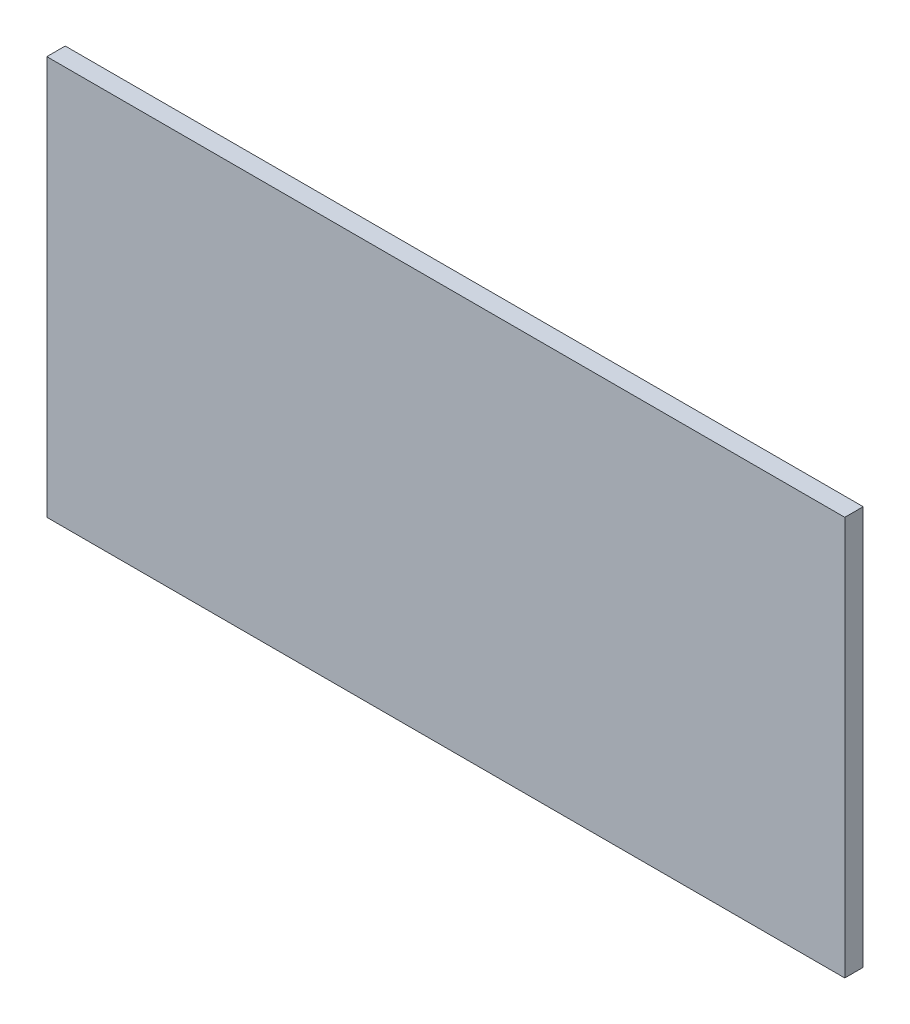
SolidWorks part; units mm, degrees
ref_plane "前视基准面" through (0, 0, 0) normal (0, 0, 1) x (1, 0, 0)
ref_plane "上视基准面" through (0, 0, 0) normal (0, 1, 0) x (1, 0, 0)
ref_plane "右视基准面" through (0, 0, 0) normal (1, 0, 0) x (0, 0, -1)
sketch "草图1" plane through (0, 0, 0) normal (0, 0, 1) x (1, 0, 0)
  line L1 (-65, 32.5) -> (65, 32.5)
  line L2 (-65, 32.5) -> (-65, -32.5)
  line L3 (-65, -32.5) -> (65, -32.5)
  line L4 (65, 32.5) -> (65, -32.5)
  line L5 (-65, 32.5) -> (65, -32.5) construction
  line L6 (-65, -32.5) -> (65, 32.5) construction
  point P0 (0, 0)
  dimension "D1" = 65
  dimension "D2" = 130
extrude "凸台-拉伸1" add sketch "草图1" along normal blind 3
